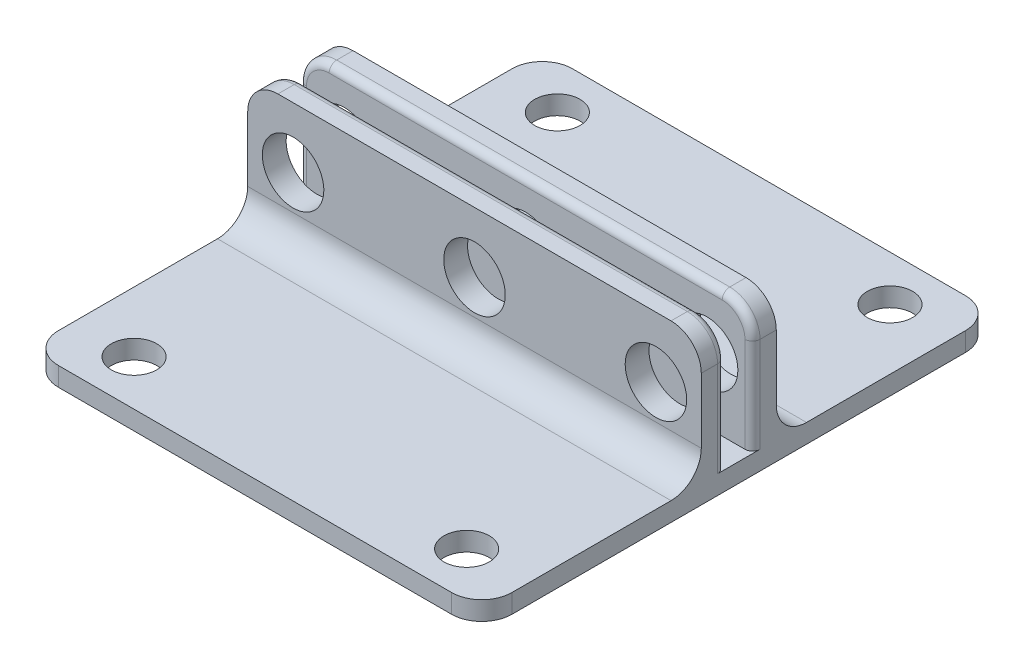
SolidWorks part; units mm, degrees
ref_plane "Front Plane" through (0, 0, 0) normal (0, 0, 1) x (1, 0, 0)
ref_plane "Top Plane" through (0, 0, 0) normal (0, 1, 0) x (1, 0, 0)
ref_plane "Right Plane" through (0, 0, 0) normal (1, 0, 0) x (0, 0, -1)
sketch "Sketch1" plane through (0, 0, 0) normal (0, 1, 0) x (1, 0, 0)
  line L0 (-33.02, 39.37) -> (-33.02, 43.18) construction
  line L1 (0, 0) -> (-38.1, 0)
  line L2 (0, 0) -> (0, 43.18)
  line L3 (0, 43.18) -> (-38.1, 43.18)
  line L4 (-38.1, 0) -> (-38.1, 43.18)
  line L5 (-33.02, 3.81) -> (-33.02, 0) construction
  line L6 (-33.02, 3.81) -> (-38.1, 3.81) construction
  line L7 (-5.08, 3.81) -> (0, 3.81) construction
  circle A0 centre (-33.02, 39.37) radius 1.905
  circle A1 centre (-33.02, 3.81) radius 1.905
  circle A2 centre (-5.08, 3.81) radius 1.905
  circle A3 centre (-5.08, 39.37) radius 1.905
  dimension "D3" = 3.81
  dimension "D1" = 38.1
  dimension "D2" = 43.18
  dimension "D4" = 27.94
  dimension "D5" = 35.56
extrude "Boss-Extrude1" add sketch "Sketch1" along normal blind 1.5875
sketch "Sketch2" plane through (-38.1, 0, 0) normal (-1, 0, 0) x (0, 0, 1)
  line L0 (-24.74, 1.5875) -> (-24.74, 12.1253)
  line L1 (-43.18, 1.5875) -> (0, 1.5875) construction
  line L2 (-24.74, 12.1253) -> (-22.74, 12.1253)
  line L3 (-22.74, 12.1253) -> (-22.74, 1.5875)
  line L4 (-22.74, 1.5875) -> (-20.44, 1.5875)
  line L5 (-20.44, 1.5875) -> (-20.44, 12.1253)
  line L6 (-20.44, 12.1253) -> (-18.44, 12.1253)
  line L7 (-18.44, 12.1253) -> (-18.44, 1.5875)
  line L8 (-18.44, 1.5875) -> (-20.44, 1.5875)
  line L9 (-22.74, 1.5875) -> (-24.74, 1.5875)
  line L10 (-43.18, 1.5875) -> (-24.74, 1.5875) construction
  line L11 (-18.44, 1.5875) -> (0, 1.5875) construction
  dimension "D1" = 2.3
  dimension "D2" = 2
  dimension "D3" = 10.5378
extrude "Boss-Extrude2" add sketch "Sketch2" against normal up to surface (38.1 mm away) contours L5 L6 L7 L8 | L9 L0 L2 L3 up to face at (0, 0.7937, -21.59)
ref_plane "Plane1" through (-38.1, 1.5875, -18.44) normal (-1, 0, 0) x (0, 0, 1)
sketch "Sketch4" plane through (0, 0, -18.44) normal (0, 0, 1) x (1, 0, 0)
  line L0 (-34.29, 7.0453) -> (-38.1, 7.0453) construction
  line L1 (-38.1, 56.5875) -> (-38.1, -53.4125) construction
  line L2 (-3.81, 7.0453) -> (0, 7.0453) construction
  line L4 (0, 12.1253) -> (-38.1, 12.1253) construction
  circle A0 centre (-34.29, 7.0453) radius 2.5828
  circle A1 centre (-19.05, 7.0453) radius 2.5828
  circle A2 centre (-3.81, 7.0453) radius 2.5828
  point P4 (0, 0)
  point P13 (0, 0)
  point P15 (0, 0)
  dimension "D1" = 5.1657
  dimension "D2" = 15.24
  dimension "D3" = 15.24
  dimension "D4" = 5.08
extrude "Cut-Extrude1" cut sketch "Sketch4" against normal through all both and the other way through all contours A0 | A1 | A2
fillet "Fillet1" radius 2.54 4 edges at (0, 12.1253, -23.74) (-38.1, 12.1253, -23.74) (0, 12.1253, -19.44) (-38.1, 12.1253, -19.44)
fillet "Fillet2" radius 2.54 2 edges at (-19.05, 1.5875, -18.44) (-19.05, 1.5875, -24.74)
fillet "Fillet4" radius 2.54 4 edges at (-38.1, 0.7937, -43.18) (0, 0.7937, -43.18) (0, 0.7937, 0) (-38.1, 0.7937, 0)
fillet "Fillet5" radius 0.635 10 edges at (0, 5.5864, -22.74) (-0.7439, 11.3814, -22.74) (-38.1, 5.5864, -22.74) (-37.3561, 11.3814, -22.74) (0, 5.5864, -20.44) (-0.7439, 11.3814, -20.44) (-38.1, 5.5864, -20.44) (-37.3561, 11.3814, -20.44) (-19.05, 12.1253, -22.74) (-19.05, 12.1253, -20.44)
